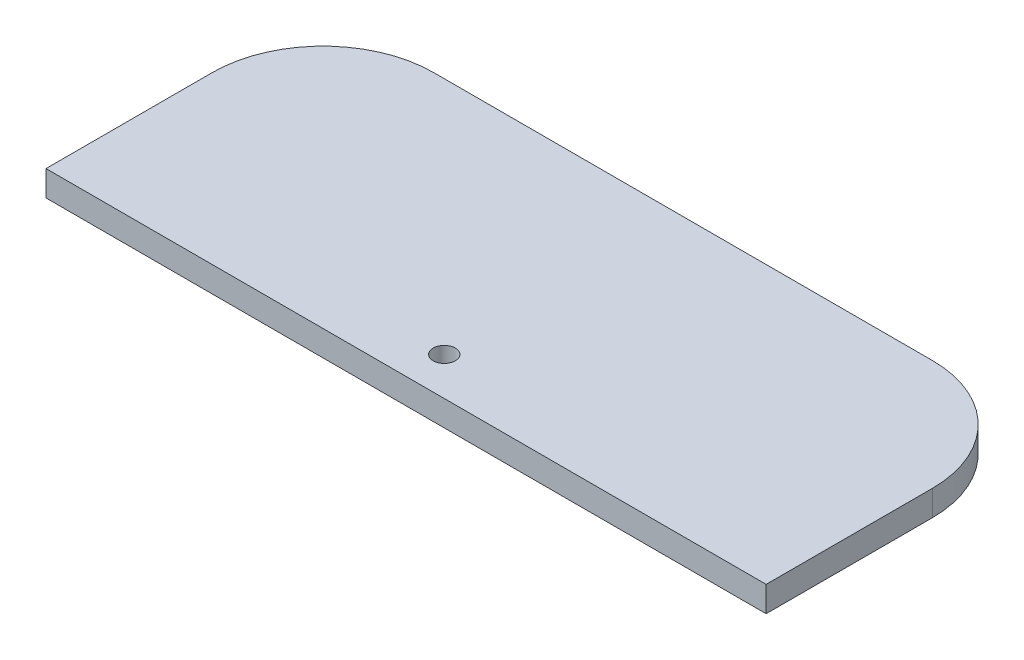
SolidWorks part; units mm, degrees
ref_plane "Front Plane" through (0, 0, 0) normal (0, 0, 1) x (1, 0, 0)
ref_plane "Top Plane" through (0, 0, 0) normal (0, 1, 0) x (1, 0, 0)
ref_plane "Right Plane" through (0, 0, 0) normal (1, 0, 0) x (0, 0, -1)
sketch "Sketch2" plane through (0, 0, 0) normal (0, 1, 0) x (1, 0, 0)
  line L1 (-32.5, 12.5) -> (32.5, 12.5)
  line L2 (-32.5, 12.5) -> (-32.5, -12.5)
  line L3 (-32.5, -12.5) -> (32.5, -12.5)
  line L4 (32.5, 12.5) -> (32.5, -12.5)
  line L5 (-32.5, 12.5) -> (32.5, -12.5) construction
  line L6 (-32.5, -12.5) -> (32.5, 12.5) construction
  circle A0 centre (0, -9.0545) radius 1
  point P0 (0, 0)
  dimension "D3" = 2
  dimension "D1" = 65
  dimension "D2" = 25
extrude "Boss-Extrude1" add sketch "Sketch2" along normal blind 2.3
fillet "Fillet9" radius 10 2 edges at (32.5, 1.15, -12.5) (-32.5, 1.15, -12.5)
